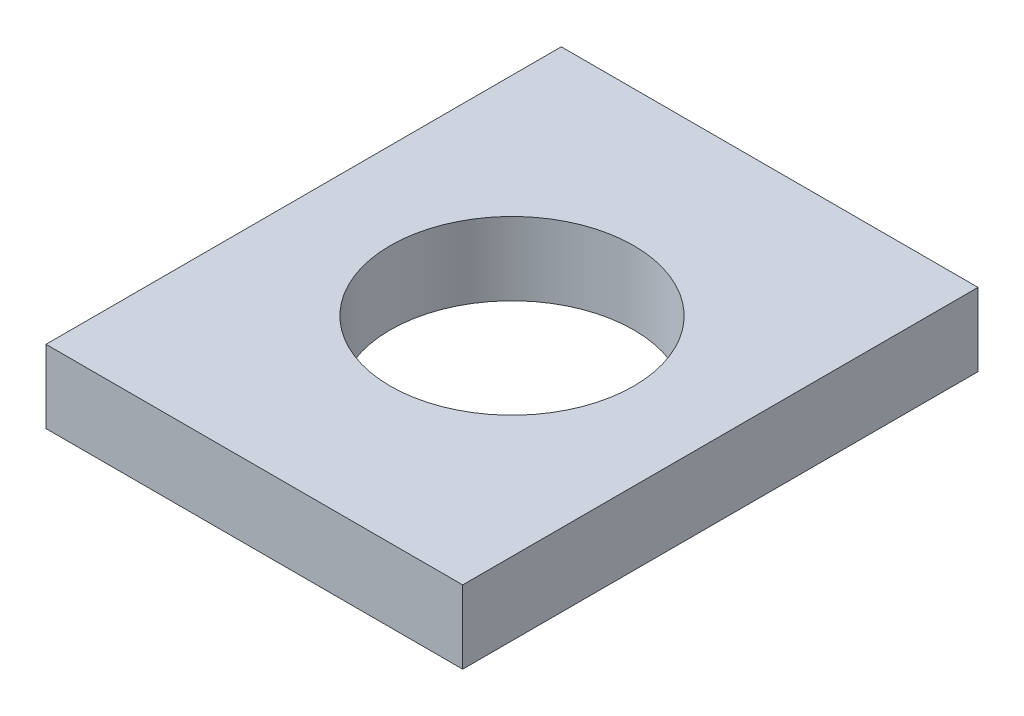
SolidWorks part; units mm, degrees
ref_plane "Front Plane" through (0, 0, 0) normal (0, 0, 1) x (1, 0, 0)
ref_plane "Top Plane" through (0, 0, 0) normal (0, 1, 0) x (1, 0, 0)
ref_plane "Right Plane" through (0, 0, 0) normal (1, 0, 0) x (0, 0, -1)
sketch "Sketch1" plane through (0, 0, 0) normal (0, 1, 0) x (1, 0, 0)
  line L1 (51.35, 63.5) -> (-51.35, 63.5)
  line L2 (51.35, 63.5) -> (51.35, -63.5)
  line L3 (51.35, -63.5) -> (-51.35, -63.5)
  line L4 (-51.35, 63.5) -> (-51.35, -63.5)
  line L5 (51.35, 63.5) -> (-51.35, -63.5) construction
  line L6 (51.35, -63.5) -> (-51.35, 63.5) construction
  point P0 (0, 0)
  dimension "D1" = 127
  dimension "D2" = 102.7
extrude "Boss-Extrude1" add sketch "Sketch1" along normal blind 18
sketch "Sketch2" plane through (0, 18, 0) normal (0, 1, 0) x (1, 0, 0)
  circle A0 centre (0, 0) radius 30
  dimension "D1" = 60
extrude "Cut-Extrude1" cut sketch "Sketch2" against normal through all
